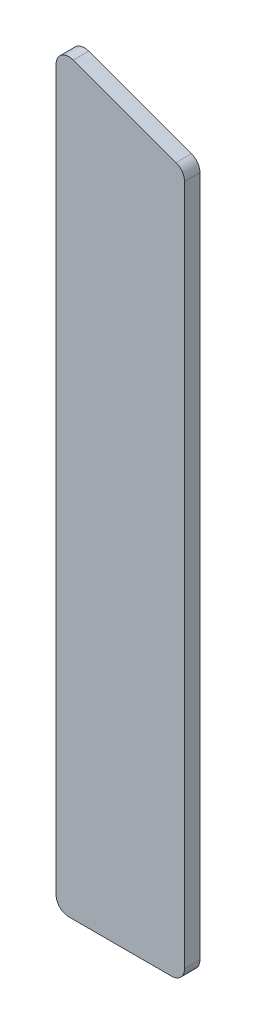
SolidWorks part; units mm, degrees
ref_plane "Plane1" through (0, 0, 0) normal (0, 0, 1) x (1, 0, 0)
ref_plane "Plane2" through (0, 0, 0) normal (0, 1, 0) x (1, 0, 0)
ref_plane "Plane3" through (0, 0, 0) normal (1, 0, 0) x (0, 0, -1)
sketch "Sketch1" plane through (0, 0, 0) normal (0, 0, 1) x (1, 0, 0)
  line L0 (0, 0) -> (0, 40) construction
  line L1 (-20, 0) -> (20, 0)
  line L2 (-25, 5) -> (-25, 285)
  line L3 (-18.2899, 289.6985) -> (21.7101, 275.1397)
  line L4 (25, 5) -> (25, 270.4412)
  arc A2 (25, 5) -> (20, 0) centre (20, 5) cw
  arc A3 (-25, 5) -> (-20, 0) centre (-20, 5) ccw
  arc A4 (-18.2899, 289.6985) -> (-25, 285) centre (-20, 285) ccw
  arc A5 (25, 270.4412) -> (21.7101, 275.1397) centre (20, 270.4412) ccw
  dimension "D6" = 5
  dimension "D2" = 290
  dimension "D1" = 50
  dimension "D7" = 70
extrude "Base-Extrude" add sketch "Sketch1" along normal blind 6
